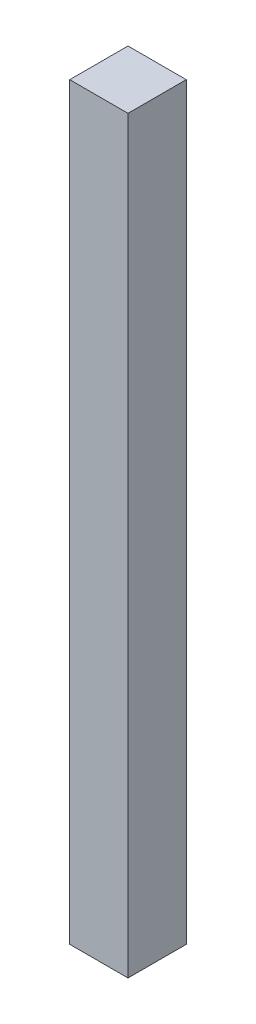
SolidWorks part; units mm, degrees
ref_plane "Plan de face" through (0, 0, 0) normal (0, 0, 1) x (1, 0, 0)
ref_plane "Plan de dessus" through (0, 0, 0) normal (0, 1, 0) x (1, 0, 0)
ref_plane "Plan de droite" through (0, 0, 0) normal (1, 0, 0) x (0, 0, -1)
sketch "Esquisse1" plane through (0, 0, 0) normal (0, 0, 1) x (1, 0, 0)
  line L1 (-73.6499, 111.4583) -> (-60.6499, 111.4583)
  line L2 (-73.6499, 111.4583) -> (-73.6499, -55.5417)
  line L3 (-73.6499, -55.5417) -> (-60.6499, -55.5417)
  line L4 (-60.6499, 111.4583) -> (-60.6499, -55.5417)
  dimension "D1" = 13
  dimension "D2" = 167
extrude "Boss.-Extru.1" add sketch "Esquisse1" along normal blind 13
equation "\"EpaisseurPlaque\"= 3"
equation "\"ProfondeurBoite\"=460"
equation "\"LongueurSyphon\"=270"
equation "\"LargeurSyphon\"=120"
equation "\"HauteurCoteDroit\"= 490"
equation "\"HauteurCoteGauche\"= 540"
equation "\"HauteurSolSyphon\"= 300"
equation "\"HauteurSyphon\"=\"HauteurCoteGauche\"-\"HauteurSolSyphon\""
equation "\"LargeurDroite\"=10"
equation "\"LargeurGauche\"=150"
equation "\"LargeurBoite\"= \"LargeurDroite\" + \"LargeurGauche\" + \"LargeurSyphon\""
equation "\"D2@Esquisse1\"=\"HauteurSyphon\" - 10  -60 -3"
